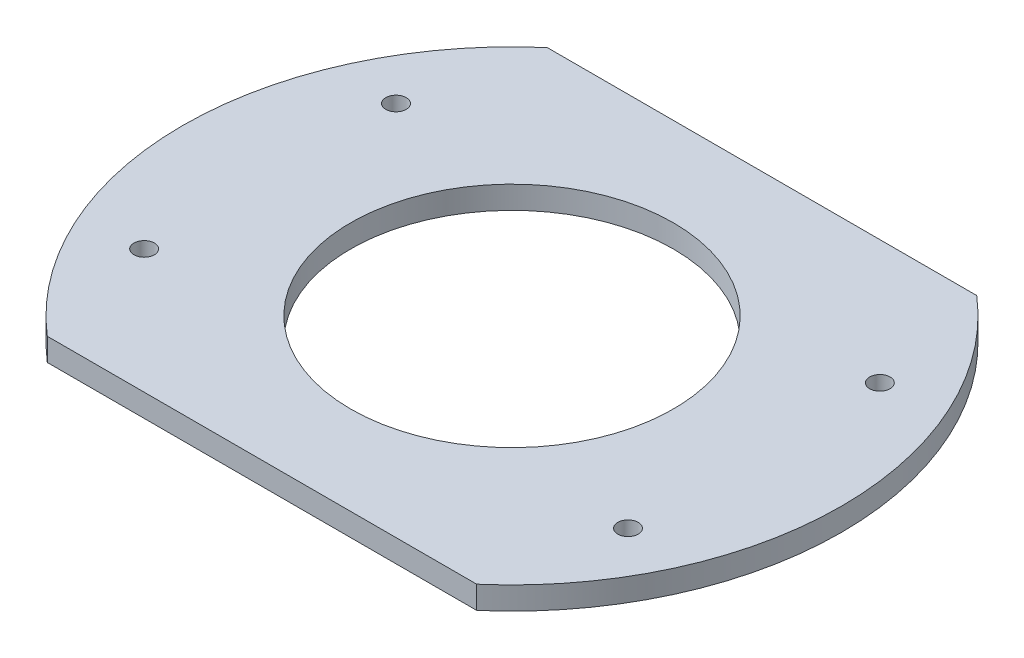
SolidWorks part; units mm, degrees
ref_plane "Спереди" through (0, 0, 0) normal (0, 0, 1) x (1, 0, 0)
ref_plane "Сверху" through (0, 0, 0) normal (0, 1, 0) x (1, 0, 0)
ref_plane "Справа" through (0, 0, 0) normal (1, 0, 0) x (0, 0, -1)
sketch "Эскиз1" plane through (0, 0, 0) normal (0, 1, 0) x (1, 0, 0)
  line L0 (-47.2361, -55) -> (47.2361, -55)
  line L1 (-47.2361, 55) -> (47.2361, 55)
  line L2 (-79.831, 41.5574) -> (79.831, -41.5574) construction
  line L3 (-84.8207, -44.1548) -> (84.8207, 44.1548) construction
  arc A0 (47.2361, -55) -> (47.2361, 55) centre (0, 0) ccw
  arc A1 (-47.2361, 55) -> (-47.2361, -55) centre (0, 0) ccw
  circle A2 centre (0, 0) radius 35.5
  circle A3 centre (0, 0) radius 60 construction
  circle A4 centre (53.2206, 27.7049) radius 2.25
  circle A5 centre (53.2206, -27.7049) radius 2.25
  circle A6 centre (-53.2206, -27.7049) radius 2.25
  circle A7 centre (-53.2206, 27.7049) radius 2.25
  point P6 (0, 0)
  point P12 (0, 0)
extrude "Бобышка-Вытянуть1" add sketch "Эскиз1" along normal blind 5
